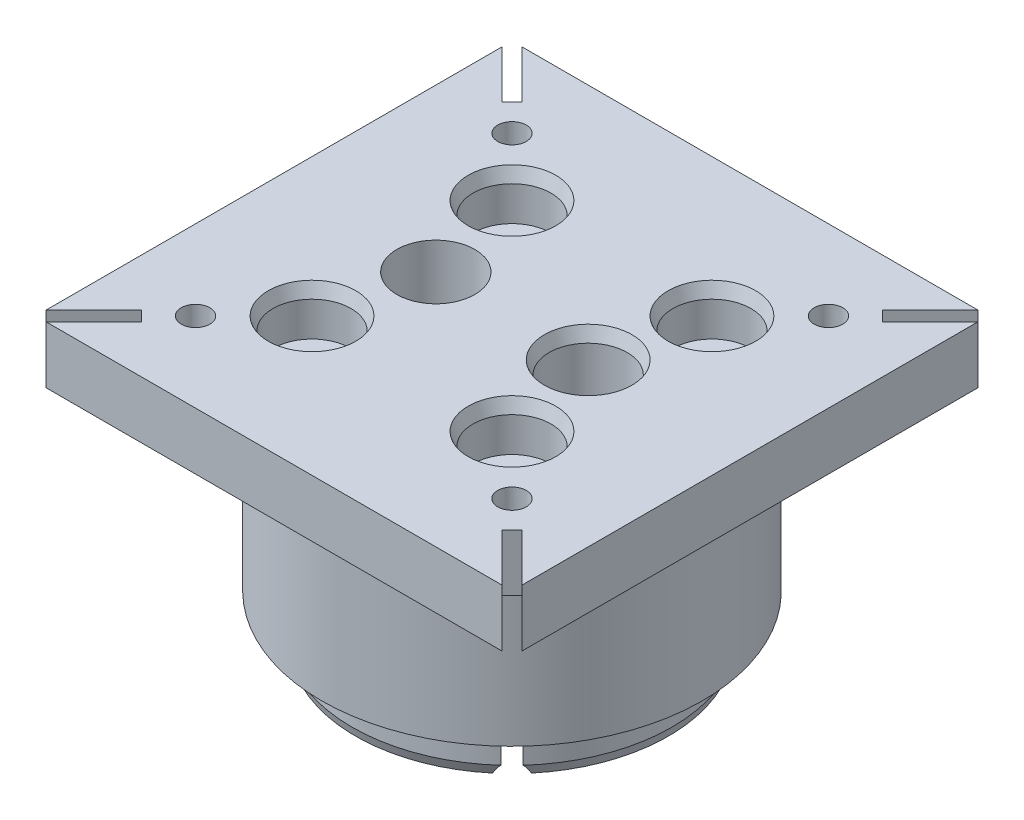
SolidWorks part; units mm, degrees
ref_plane "Спереди" through (0, 0, 0) normal (0, 0, 1) x (1, 0, 0)
ref_plane "Сверху" through (0, 0, 0) normal (0, 1, 0) x (1, 0, 0)
ref_plane "Справа" through (0, 0, 0) normal (1, 0, 0) x (0, 0, -1)
sketch "Sketch1" plane through (0, 0, 0) normal (0, 1, 0) x (1, 0, 0)
  circle A0 centre (0, 0) radius 20
  dimension "D1" = 40
extrude "Boss-Extrude1" add sketch "Sketch1" along normal blind 25
sketch "Sketch3" plane through (0, 0, 0) normal (0, -1, 0) x (1, 0, 0)
  circle A0 centre (0, 0) radius 16.8
  circle A1 centre (0, 0) radius 20 construction
  dimension "D1" = 3.2
extrude "Boss-Extrude2" add sketch "Sketch3" along normal blind 5
sketch "Sketch4" plane through (0, 25, 0) normal (0, 1, 0) x (1, 0, 0)
  line L0 (20, 0) -> (-20, 0) construction
  line L1 (2.8, 5.2) -> (13.2, 5.2) construction
  line L2 (2.8, 5.2) -> (2.8, -5.2) construction
  line L3 (2.8, -5.2) -> (13.2, -5.2) construction
  line L4 (13.2, 5.2) -> (13.2, -5.2) construction
  line L5 (2.8, 5.2) -> (13.2, -5.2) construction
  line L6 (2.8, -5.2) -> (13.2, 5.2) construction
  circle A0 centre (8, 0) radius 4.1
  circle A1 centre (0, 0) radius 20 construction
  circle A2 centre (-8, 0) radius 4.1
  point P0 (8, 0)
  point P9 (0, 0)
  dimension "D2" = 8.2
  dimension "D4" = 16
  dimension "D1" = 10.4
  dimension "D3" = 8
extrude "Cut-Extrude1" cut sketch "Sketch4" against normal through all
sketch "Sketch6" plane through (0, 25, 0) normal (0, 1, 0) x (1, 0, 0)
  line L1 (-10.5, 10.5) -> (10.5, 10.5) construction
  line L2 (-10.5, 10.5) -> (-10.5, -10.5) construction
  line L3 (-10.5, -10.5) -> (10.5, -10.5) construction
  line L4 (10.5, 10.5) -> (10.5, -10.5) construction
  line L5 (-10.5, 10.5) -> (10.5, -10.5) construction
  line L6 (-10.5, -10.5) -> (10.5, 10.5) construction
  circle A0 centre (10.5, -10.5) radius 2.1
  circle A1 centre (-10.5, -10.5) radius 2.1
  circle A2 centre (-10.5, 10.5) radius 2.1
  circle A3 centre (10.5, 10.5) radius 2.1
  point P0 (0, 0)
  dimension "D1" = 4.2
  dimension "D2" = 21
extrude "Cut-Extrude2" cut sketch "Sketch6" against normal through all
chamfer "Chamfer1" distance 1 angle 20 4 edges at (16.8, -5, 0) (0, -5, -16.8) (-16.8, -5, 0) (0, -5, 16.8)
sketch "Sketch7" plane through (0, 25, 0) normal (0, 1, 0) x (1, 0, 0)
  circle A0 centre (10.5, 10.5) radius 4.1
  circle A1 centre (-10.5, 10.5) radius 4.1
  circle A2 centre (-10.5, -10.5) radius 4.1
  circle A3 centre (10.5, -10.5) radius 4.1
  dimension "D1" = 8.2
extrude "Cut-Extrude3" cut sketch "Sketch7" against normal blind 5
chamfer "Chamfer2" distance 0.5 angle 70 1 edges at (8, 25, 4.1)
sketch "Sketch8" plane through (0, 25, 0) normal (0, 1, 0) x (1, 0, 0)
  line L1 (25, 25) -> (-25, 25)
  line L2 (25, 25) -> (25, -25)
  line L3 (25, -25) -> (-25, -25)
  line L4 (-25, 25) -> (-25, -25)
  line L5 (25, 25) -> (-25, -25) construction
  line L6 (25, -25) -> (-25, 25) construction
  circle A0 centre (0, 0) radius 20
  circle A1 centre (0, 0) radius 20 construction
  circle A2 centre (-16.617, -16.617) radius 1.5
  circle A3 centre (-16.617, 16.617) radius 1.5
  circle A4 centre (16.617, 16.617) radius 1.5
  circle A5 centre (16.617, -16.617) radius 1.5
  circle A6 centre (0, 0) radius 23.5 construction
  circle M12 centre (0, 0) radius 20
  dimension "D1" = 3
  dimension "D2" = 47
  dimension "D3" = 50
extrude "Boss-Extrude3" add sketch "Sketch8" against normal blind 6 contours L4 L3 A2 M12 | L3 L2 A5 M12 | L2 L1 A4 M12 | L1 L4 A3 M12
sketch "Sketch10" plane through (0, 25, 0) normal (0, 1, 0) x (1, 0, 0)
  line L0 (-25, -25) -> (25, 25) construction
  line L1 (-25, 25) -> (25, -25) construction
  line L2 (-19.9758, -18.9151) -> (-18.9151, -19.9758)
  line L3 (-18.9151, -19.9758) -> (-23.9393, -25)
  line L4 (25, -25) -> (-25, -25) construction
  line L5 (-23.9393, -25) -> (-25, -25)
  line L6 (-25, -25) -> (-25, -23.9393)
  line L7 (-25, -23.9393) -> (-19.9758, -18.9151)
  line L8 (-25, 23.9393) -> (-19.9758, 18.9151)
  line L9 (-25, 25) -> (-25, -25) construction
  line L10 (-19.9758, 18.9151) -> (-18.9151, 19.9758)
  line L11 (-18.9151, 19.9758) -> (-23.9393, 25)
  line L12 (25, 25) -> (-25, 25) construction
  line L13 (-23.9393, 25) -> (-25, 25)
  line L14 (-25, 25) -> (-25, 23.9393)
  line L15 (23.9393, 25) -> (18.9151, 19.9758)
  line L16 (18.9151, 19.9758) -> (19.9758, 18.9151)
  line L17 (19.9758, 18.9151) -> (25, 23.9393)
  line L18 (25, 25) -> (25, -25) construction
  line L19 (25, 23.9393) -> (25, 25)
  line L20 (25, 25) -> (23.9393, 25)
  line L21 (18.9151, -19.9758) -> (19.9758, -18.9151)
  line L22 (19.9758, -18.9151) -> (25, -23.9393)
  line L23 (25, -23.9393) -> (25, -25)
  line L24 (25, -25) -> (23.9393, -25)
  line L25 (23.9393, -25) -> (18.9151, -19.9758)
  circle A0 centre (-16.617, -16.617) radius 1.5 construction
  point P10 (-19.4454, -19.4454)
  point P19 (-19.4454, 19.4454)
  point P26 (19.4454, 19.4454)
  point P33 (19.4454, -19.4454)
  dimension "D1" = 4
  dimension "D2" = 1.5
extrude "Cut-Extrude4" cut sketch "Sketch10" against normal through all
chamfer "Chamfer3" distance 0.5 angle 70 4 edges at (10.5, 25, -6.4) (-10.5, 25, -6.4) (-10.5, 25, 14.6) (10.5, 25, 14.6)
sketch "Sketch11" plane through (0, -5, 0) normal (0, -1, 0) x (1, 0, 0)
  line L1 (-8, 7.5) -> (-14.4952, 3.75)
  line L2 (-14.4952, 3.75) -> (-14.4952, -3.75)
  line L3 (-14.4952, -3.75) -> (-8, -7.5)
  line L4 (-8, -7.5) -> (-1.5048, -3.75)
  line L5 (-1.5048, -3.75) -> (-1.5048, 3.75)
  line L6 (-1.5048, 3.75) -> (-8, 7.5)
  line L7 (-16.436, 0) -> (16.436, 0) construction
  line L9 (8, 7.5) -> (1.5048, 3.75)
  line L10 (1.5048, 3.75) -> (1.5048, -3.75)
  line L11 (1.5048, -3.75) -> (8, -7.5)
  line L12 (8, -7.5) -> (14.4952, -3.75)
  line L13 (14.4952, -3.75) -> (14.4952, 3.75)
  line L14 (14.4952, 3.75) -> (8, 7.5)
  circle A0 centre (-8, 0) radius 7.5 construction
  circle A1 centre (0, 0) radius 16.436 construction
  circle A2 centre (8, 0) radius 7.5 construction
  point P1 (-8.2501, -7.4958)
  point P10 (1.4985, 3.7391)
  point P11 (0, 0)
  dimension "D1" = 15
  dimension "D2" = 16
  dimension "D3" = 8
extrude "Cut-Extrude5" cut sketch "Sketch11" against normal blind 6.5
chamfer "Chamfer4" distance 1 angle 45 13 edges at (-11.2476, -5, 5.625) (-14.4952, -5, 0) (-11.2476, -5, -5.625) (-4.7524, -5, -5.625) (-1.5048, -5, 0) (-4.7524, -5, 5.625) (0, 19, 20) (4.7524, -5, 5.625) (1.5048, -5, 0) (4.7524, -5, -5.625) (11.2476, -5, -5.625) (14.4952, -5, 0) (11.2476, -5, 5.625)
